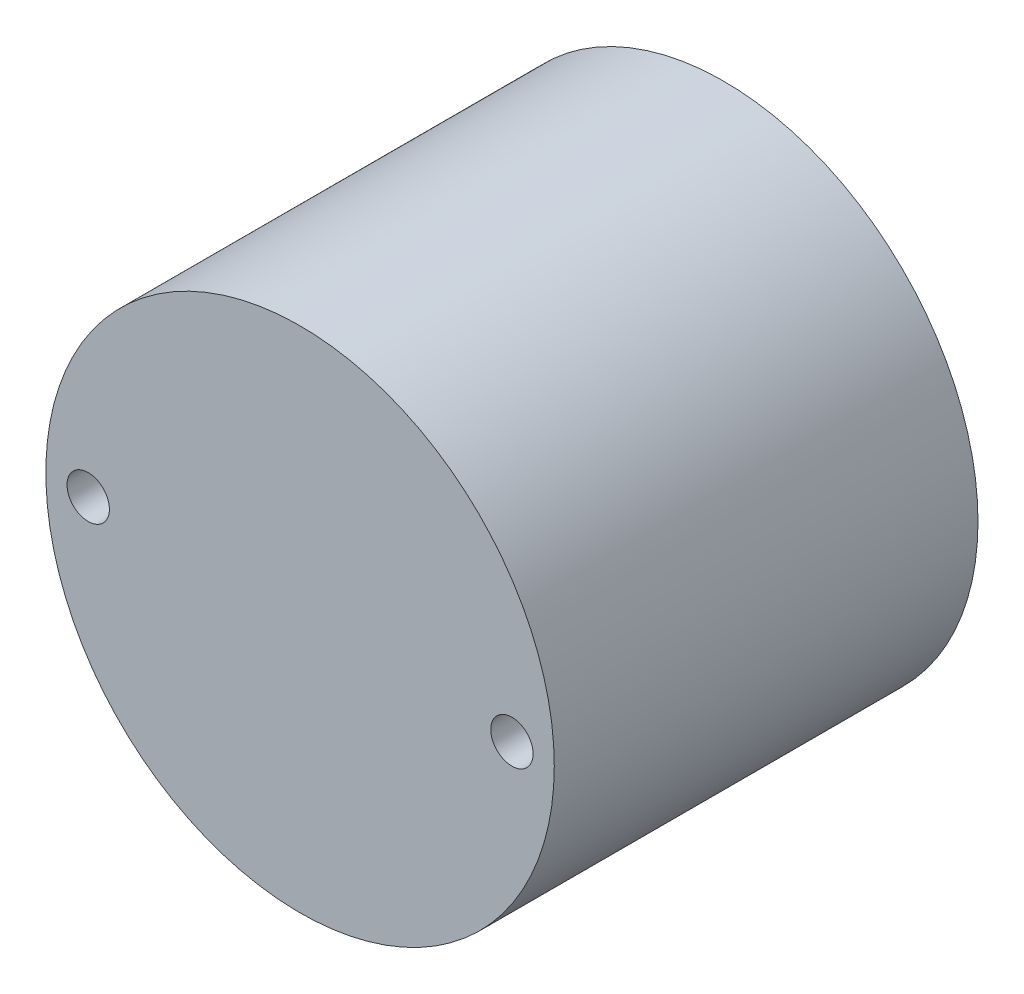
SolidWorks part; units mm, degrees
ref_plane "Front Plane" through (0, 0, 0) normal (0, 0, 1) x (1, 0, 0)
ref_plane "Top Plane" through (0, 0, 0) normal (0, 1, 0) x (1, 0, 0)
ref_plane "Right Plane" through (0, 0, 0) normal (1, 0, 0) x (0, 0, -1)
imported_body "Imported7" [suppressed]
sketch "Sketch1" [suppressed] plane through (0, 11.25, 0) normal (0, -1, 0) x (1, 0, 0)
  circle A0 centre (10.1, 0) radius 6
  circle A1 centre (15.1, 0) radius 0.5
  circle A2 centre (5.1, 0) radius 0.5
  dimension "D1" = 12
  dimension "D2" = 1
  dimension "D3" = 1
  dimension "D4" = 5
  dimension "D5" = 5
extrude "Boss-Extrude1" [suppressed] add sketch "Sketch1" along normal blind 10
sketch "Sketch2" plane through (0, 0, 0) normal (0, 0, 1) x (1, 0, 0)
  circle A0 centre (0, 0) radius 6
  circle A1 centre (-5, 0) radius 0.5
  circle A2 centre (5, 0) radius 0.5
  dimension "D1" = 12
  dimension "D2" = 1
  dimension "D3" = 1
  dimension "D4" = 5
  dimension "D5" = 5
extrude "Boss-Extrude2" add sketch "Sketch2" along normal blind 10
